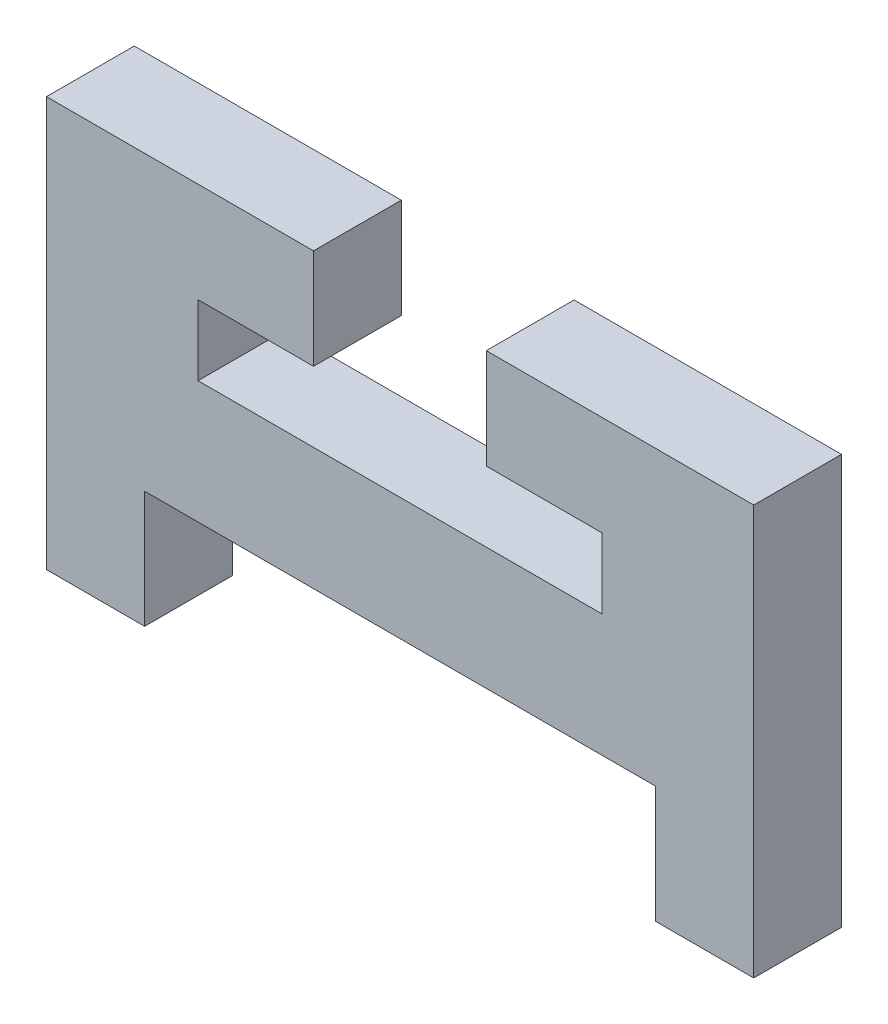
SolidWorks part; units mm, degrees
ref_plane "Alzado" through (0, 0, 0) normal (0, 0, 1) x (1, 0, 0)
ref_plane "Planta" through (0, 0, 0) normal (0, 1, 0) x (1, 0, 0)
ref_plane "Vista lateral" through (0, 0, 0) normal (1, 0, 0) x (0, 0, -1)
sketch "Model" plane through (0, 0, 0) normal (0, 0, 1) x (1, 0, 0)
  line L0 (31.7, 16.7827) -> (24.2933, 16.7827)
  line L1 (24.2933, 16.7827) -> (24.2933, 19.1827)
  line L2 (24.2933, 19.1827) -> (28.24, 19.1827)
  line L3 (28.24, 19.1827) -> (28.24, 22.6)
  line L4 (28.24, 22.6) -> (19.1133, 22.6)
  line L5 (19.1133, 22.6) -> (19.1133, 8.6)
  line L6 (19.1133, 8.6) -> (22.468, 8.6)
  line L7 (22.468, 8.6) -> (22.468, 12.6)
  line L8 (22.468, 12.6) -> (39.932, 12.6)
  line L9 (39.932, 12.6) -> (39.932, 8.6)
  line L10 (39.932, 8.6) -> (43.2867, 8.6)
  line L11 (43.2867, 8.6) -> (43.2867, 22.6)
  line L12 (43.2867, 22.6) -> (34.1466, 22.6)
  line L13 (34.1466, 22.6) -> (34.1466, 19.1827)
  line L14 (34.1466, 19.1827) -> (38.1067, 19.1827)
  line L15 (38.1067, 19.1827) -> (38.1067, 16.7827)
  line L16 (38.1067, 16.7827) -> (31.7, 16.7827)
extrude "Saliente-Extruir1" add sketch "Model" along normal blind 3
